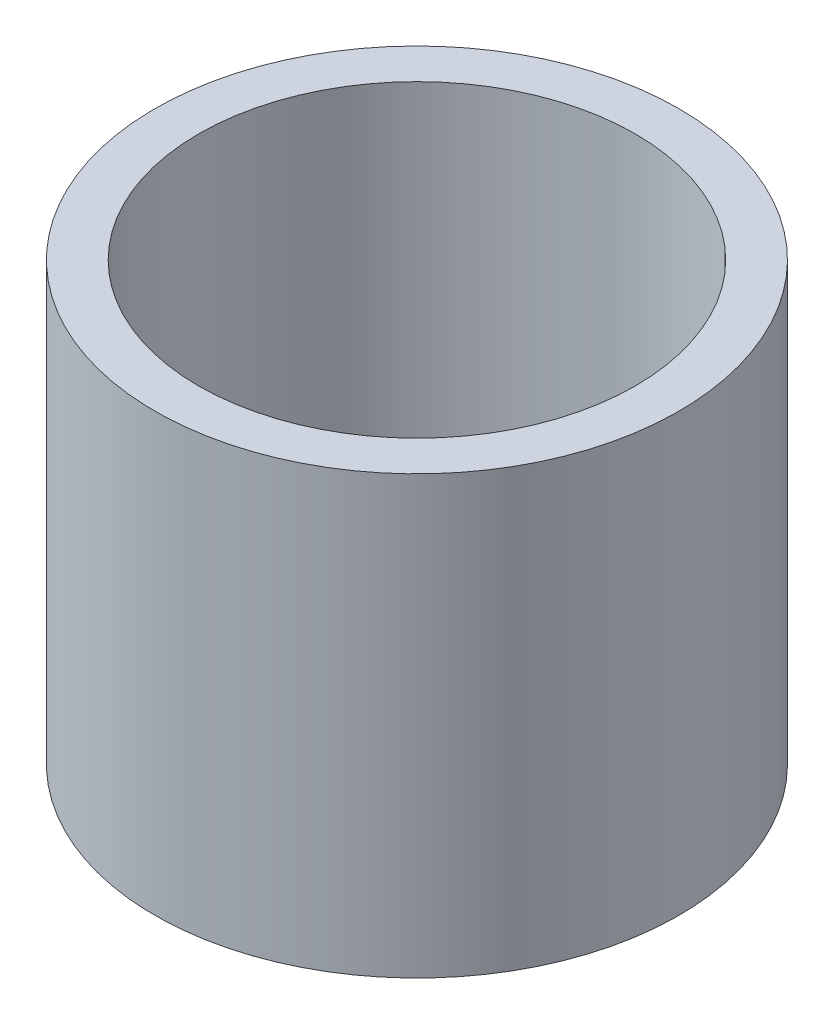
SolidWorks part; units mm, degrees
material "Laiton"
ref_plane "Plan de face" through (0, 0, 0) normal (0, 0, 1) x (1, 0, 0)
ref_plane "Plan de dessus" through (0, 0, 0) normal (0, 1, 0) x (1, 0, 0)
ref_plane "Plan de droite" through (0, 0, 0) normal (1, 0, 0) x (0, 0, -1)
sketch "Esquisse1" plane through (0, 0, 0) normal (0, 0, 1) x (1, 0, 0)
  line L0 (0, -15.8878) -> (0, 19.7449) construction
  line L1 (-5, 10) -> (-6, 10)
  line L4 (-6, 10) -> (-6, 0)
  line L5 (-6, 0) -> (-5, 0)
  line L6 (-5, 0) -> (-5, 10)
  dimension "D2" = 10
  dimension "D4" = 6
  dimension "D5" = 5
  dimension "D6" = 0
revolve "Révolution1" add sketch "Esquisse1" angle 360 about L0
